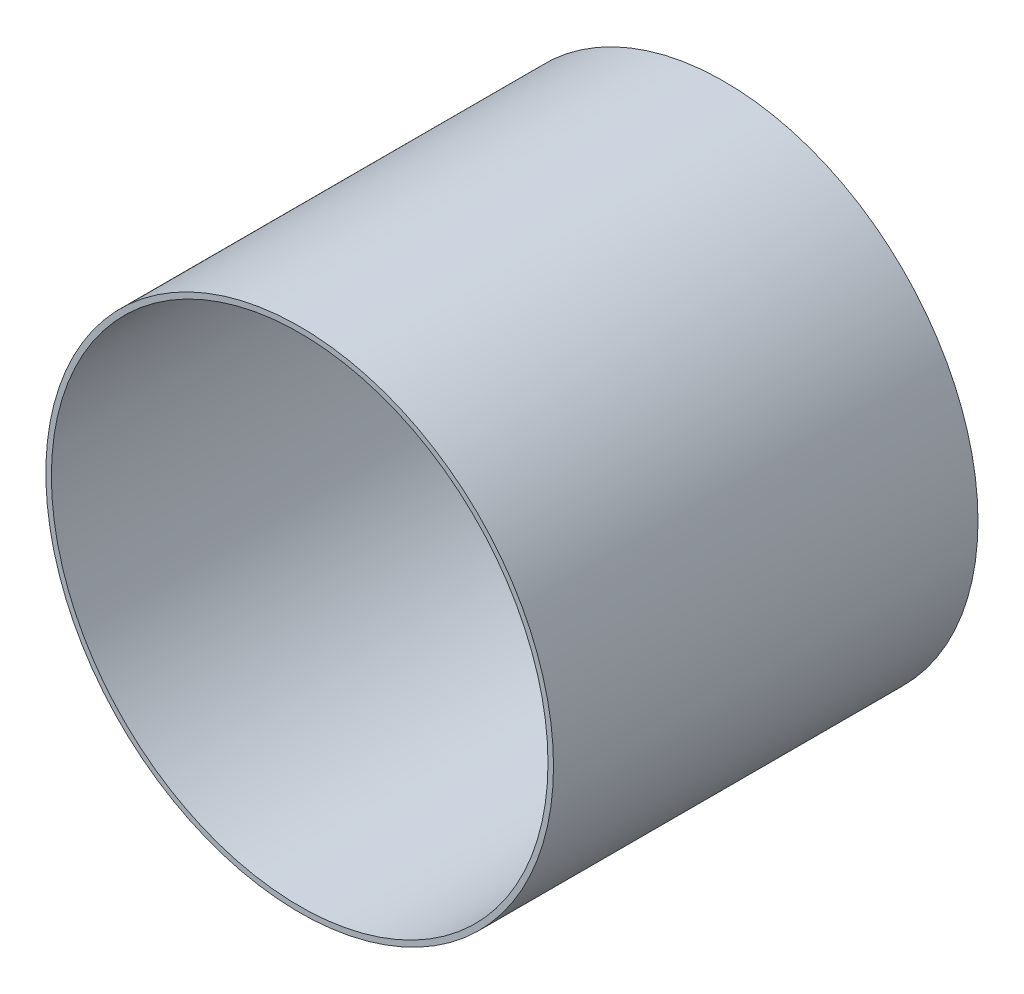
SolidWorks part; units mm, degrees
material "E-Glass Fiber"
ref_plane "Front Plane" through (0, 0, 0) normal (0, 0, 1) x (1, 0, 0)
ref_plane "Top Plane" through (0, 0, 0) normal (0, 1, 0) x (1, 0, 0)
ref_plane "Right Plane" through (0, 0, 0) normal (1, 0, 0) x (0, 0, -1)
sketch "Sketch1" plane through (0, 0, 0) normal (0, 0, 1) x (1, 0, 0)
  circle A0 centre (0, 0) radius 74.295
  circle A1 centre (0, 0) radius 75.946
  dimension "D1" = 148.59
  dimension "D2" = 151.892
extrude "Boss-Extrude1" add sketch "Sketch1" along normal blind 127
